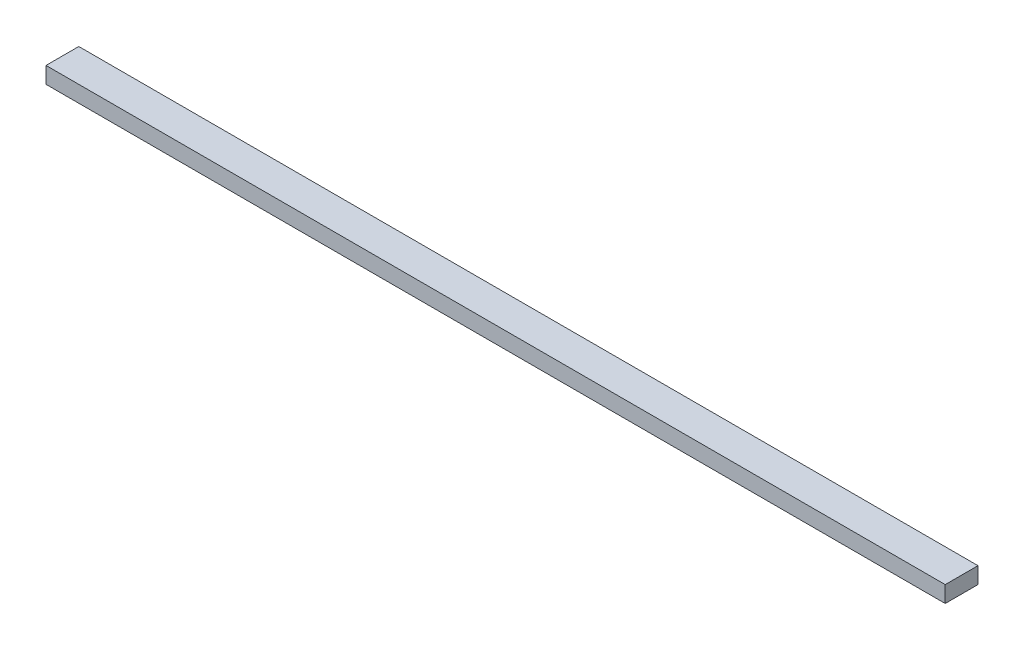
SolidWorks part; units mm, degrees
ref_plane "Front Plane" through (0, 0, 0) normal (0, 0, 1) x (1, 0, 0)
ref_plane "Top Plane" through (0, 0, 0) normal (0, 1, 0) x (1, 0, 0)
ref_plane "Right Plane" through (0, 0, 0) normal (1, 0, 0) x (0, 0, -1)
sketch "Sketch1" plane through (0, 0, 0) normal (0, 1, 0) x (1, 0, 0)
  line L0 (-274.265, 10) -> (274.265, -10) construction
  line L1 (-274.265, 10) -> (274.265, 10)
  line L2 (-274.265, 10) -> (-274.265, -10)
  line L3 (-274.265, -10) -> (274.265, -10)
  line L4 (274.265, 10) -> (274.265, -10)
  dimension "D1" = 548.53
  dimension "D2" = 20
extrude "Boss-Extrude1" add sketch "Sketch1" along normal blind 10
